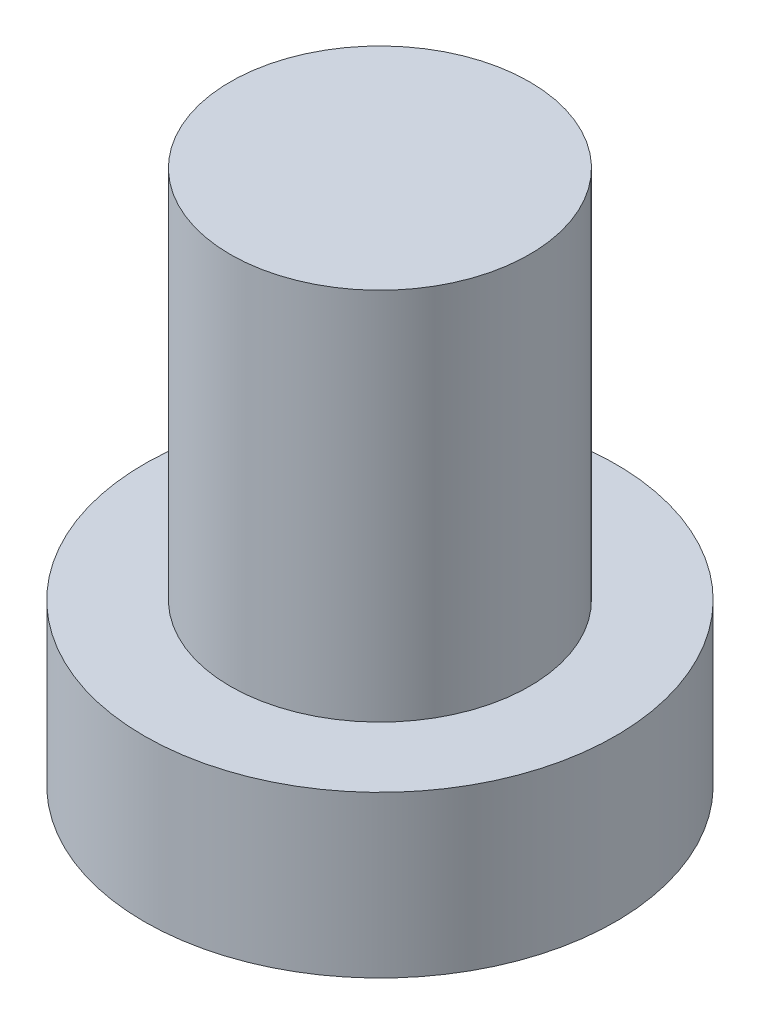
SolidWorks part; units mm, degrees
ref_plane "前视基准面" through (0, 0, 0) normal (0, 0, 1) x (1, 0, 0)
ref_plane "上视基准面" through (0, 0, 0) normal (0, 1, 0) x (1, 0, 0)
ref_plane "右视基准面" through (0, 0, 0) normal (1, 0, 0) x (0, 0, -1)
sketch "草图1" plane through (0, 0, 0) normal (0, 1, 0) x (1, 0, 0)
  circle A0 centre (0, 0) radius 3.15
extrude "凸台-拉伸1" add sketch "草图1" along normal blind 2.15
sketch "草图2" plane through (0, 2.15, 0) normal (0, 1, 0) x (1, 0, 0)
  circle A0 centre (0, 0) radius 2
extrude "凸台-拉伸2" add sketch "草图2" along normal blind 5
sketch "草图3" plane through (0, 0, 0) normal (0, -1, 0) x (1, 0, 0)
  line L0 (-0.5, 1) -> (-0.5, 2)
  line L1 (-2, -0.5) -> (-1, -0.5)
  line L2 (-2, -0.5) -> (-2, 0.5)
  line L3 (-2, 0.5) -> (-1, 0.5)
  line L4 (2, -0.5) -> (2, 0.5)
  line L5 (-2, -0.5) -> (2, 0.5) construction
  line L6 (-2, 0.5) -> (2, -0.5) construction
  line L7 (-0.5, -2) -> (0.5, -2)
  line L8 (-0.5, -2) -> (-0.5, -1)
  line L9 (-0.5, 2) -> (0.5, 2)
  line L10 (0.5, -2) -> (0.5, -1)
  line L11 (-0.5, -2) -> (0.5, 2) construction
  line L12 (-0.5, 2) -> (0.5, -2) construction
  line L13 (1, -0.5) -> (2, -0.5)
  line L14 (0.5, 1) -> (0.5, 2)
  line L15 (1, 0.5) -> (2, 0.5)
  arc A0 (-0.5, -1) -> (-1, -0.5) centre (-1, -1) ccw
  arc A1 (1, -0.5) -> (0.5, -1) centre (1, -1) ccw
  arc A2 (0.5, 1) -> (1, 0.5) centre (1, 1) ccw
  arc A3 (-0.5, 1) -> (-1, 0.5) centre (-1, 1) cw
  point P0 (0, 0)
  point P6 (0, 0)
  point P21 (0.5, 0.5)
  dimension "D1" = 0.5
extrude "切除-拉伸1" cut sketch "草图3" against normal blind 1.5
